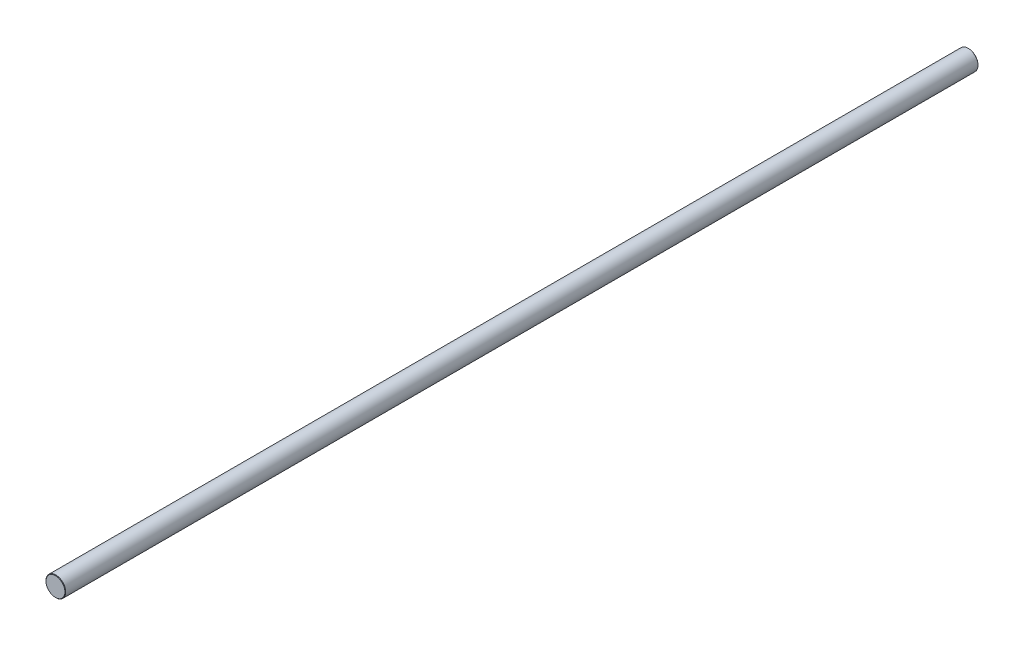
SolidWorks part; units mm, degrees
ref_plane "Front Plane" through (0, 0, 0) normal (0, 0, 1) x (1, 0, 0)
ref_plane "Top Plane" through (0, 0, 0) normal (0, 1, 0) x (1, 0, 0)
ref_plane "Right Plane" through (0, 0, 0) normal (1, 0, 0) x (0, 0, -1)
sketch "Sketch1" plane through (0, 0, 0) normal (0, 0, 1) x (1, 0, 0)
  circle A0 centre (0, 0) radius 4 construction
  dimension "Diameter" = 8
sketch "Sketch2" plane through (0, 0, 0) normal (1, 0, 0) x (0, 0, -1)
  line L0 (185, 0) -> (-185, 0) construction
  point P0 (-148, 0)
  point P3 (0, 0)
  point P4 (148, 0)
  point P6 (-129.5, 0)
  point P7 (129.5, 0)
  dimension "Length" = 370
  dimension "D1" = 37
  dimension "D2" = 37
  dimension "D3" = 55.5
  dimension "D4" = 55.5
sketch "Sketch3" plane through (0, 0, 0) normal (0, 0, 1) x (1, 0, 0)
  circle A0 centre (0, 0) radius 4 construction
  circle A1 centre (0, 0) radius 4
extrude "Boss-Extrude1" add sketch "Sketch3" along normal up to vertex (185 mm away) and the other way up to vertex (185 mm away) up to point (0, 0, 185) other way up to point (0, 0, -185)
chamfer "Chamfer1" distance 0.16 angle 45 2 edges at (4, 0, 185) (4, 0, -185)
equation "\"D1@Chamfer1\"=\"Diameter@Sketch1\"*.02"
equation "\"D1@Sketch2\"=\"D2@Sketch2\""
equation "\"D2@Sketch2\"=\"Length@Sketch2\"*.1"
equation "\"D3@Sketch2\"=\"Length@Sketch2\"*.15"
equation "\"D4@Sketch2\"=\"D3@Sketch2\""
